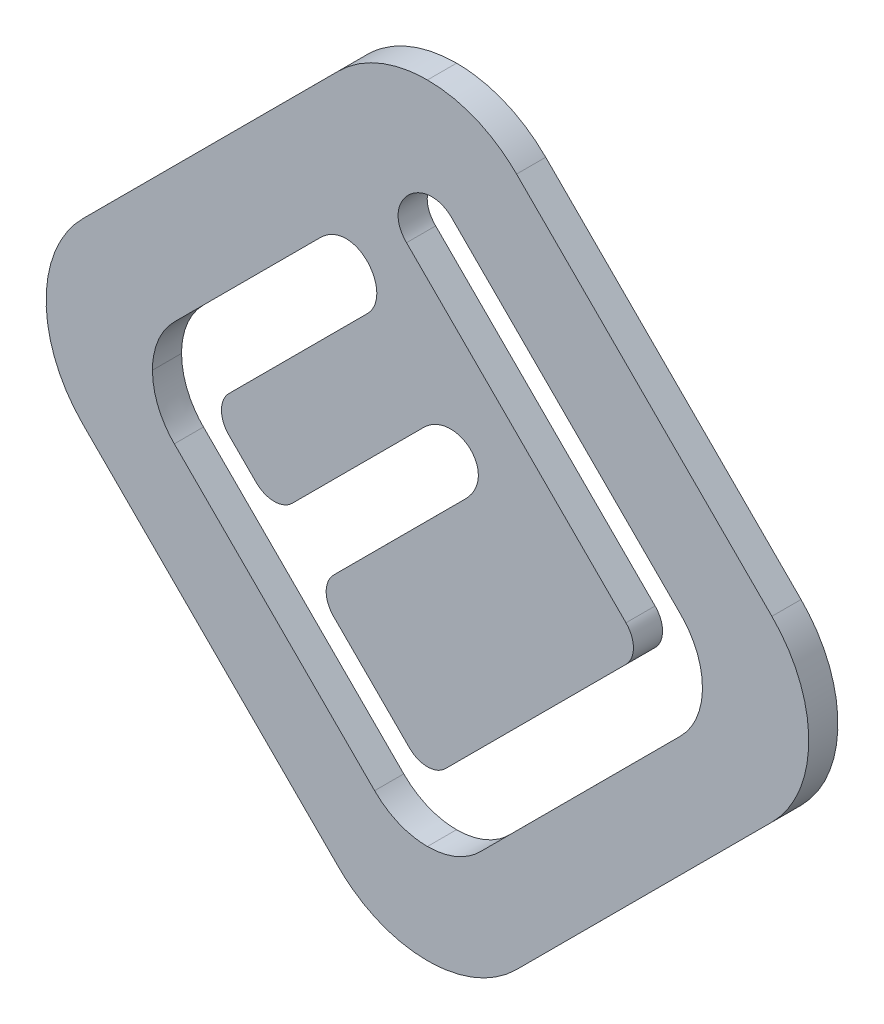
SolidWorks part; units mm, degrees
material "Maple"
ref_plane "Front Plane" through (0, 0, 0) normal (0, 0, 1) x (1, 0, 0)
ref_plane "Top Plane" through (0, 0, 0) normal (0, 1, 0) x (1, 0, 0)
ref_plane "Right Plane" through (0, 0, 0) normal (1, 0, 0) x (0, 0, -1)
sketch "Sketch1" plane through (0, 0, 317.1825) normal (0, 0, 1) x (1, 0, 0)
  line L8 (18.0256, -0.3675) -> (4.6642, 12.994)
  line L9 (-4.6636, 12.994) -> (-18.0256, -0.3674)
  line L10 (-18.0253, -9.6953) -> (-4.6635, -23.0569)
  line L11 (4.6641, -23.0569) -> (18.0256, -9.6953)
  line L12 (18.0256, -0.3675) -> (4.6642, 12.994)
  line L13 (-4.6636, 12.994) -> (-18.0256, -0.3674)
  line L14 (-18.0253, -9.6953) -> (-4.6635, -23.0569)
  line L15 (4.6641, -23.0569) -> (18.0256, -9.6953)
  line L22 (2.7642, -18.6667) -> (13.244, -8.1858)
  line L23 (10.3894, -6.365) -> (0.9434, -15.8112)
  line L24 (-0.9425, -15.8112) -> (-4.9072, -11.8463)
  line L25 (-8.9601, -7.7941) -> (-10.3892, -6.3639)
  line L26 (-13.2442, -8.1856) -> (-2.7641, -18.665)
  line L27 (2.7642, -18.6667) -> (13.244, -8.1858)
  line L28 (10.3894, -6.365) -> (0.9434, -15.8112)
  line L29 (-0.9425, -15.8112) -> (-4.9072, -11.8463)
  line L30 (-8.9601, -7.7941) -> (-10.3892, -6.3639)
  line L31 (-13.2442, -8.1856) -> (-2.7641, -18.665)
  arc A10 (-10.3887, -4.4783) -> (-10.3892, -6.3639) centre (-9.4459, -5.4213) ccw
  arc A11 (-10.3887, -4.4783) -> (-10.3892, -6.3639) centre (-9.4459, -5.4213) ccw
  arc A12 (10.3894, -6.365) -> (10.3894, -4.4792) centre (9.4465, -5.4221) ccw
  arc A13 (10.3894, -6.365) -> (10.3894, -4.4792) centre (9.4465, -5.4221) ccw
  arc A14 (-0.9425, -15.8112) -> (0.9434, -15.8112) centre (0.0004, -14.8683) ccw
  arc A15 (-0.9425, -15.8112) -> (0.9434, -15.8112) centre (0.0004, -14.8683) ccw
  arc A16 (-4.9072, -9.9604) -> (-4.9072, -11.8463) centre (-3.9643, -10.9034) ccw
  arc A17 (-4.9072, -9.9604) -> (-4.9072, -11.8463) centre (-3.9643, -10.9034) ccw
  arc A18 (-8.9601, -7.7941) -> (-7.074, -7.7946) centre (-8.0168, -6.8515) ccw
  arc A19 (-8.9601, -7.7941) -> (-7.074, -7.7946) centre (-8.0168, -6.8515) ccw
  spline S12 degree 3 poles (-2511.7582, 1599.7542) (-528.2673, 253.9159) (-9.7312, -51.3951) (18.9649, -8.5195) (19.0757, -8.335) (19.2797, -7.9533) (19.3731, -7.7556) (19.6204, -7.1566) (19.7443, -6.7455) (19.9118, -5.9003) (19.9545, -5.4636) (19.9548, -4.6035) (19.9137, -4.1758) (19.7883, -3.5377) (19.7358, -3.3259) (19.6114, -2.9129) (19.5394, -2.7105) (19.2943, -2.1153) (19.0909, -1.7324) (-37.9766, 83.7462) (-1962.1181, -1327.3743) (2142.1316, 2091.9164) knots -14.829429 -14.829429 -14.829429 -14.829429 0.125 0.125 0.1875 0.1875 0.25 0.25 0.375 0.375 0.5 0.5 0.625 0.625 0.6875 0.6875 0.75 0.75 0.875 0.875 30.319445 30.319445 30.319445 30.319445 only from (18.0256, -9.6953) to (18.0256, -0.3675)
  spline S13 degree 3 poles (2060.8953, 2183.1746) (-826.604, -1283.2725) (72.1685, -32.1264) (3.3032, 14.0591) (2.9215, 14.2633) (2.3277, 14.5093) (2.1257, 14.5816) (1.7134, 14.7064) (1.502, 14.759) (-86.1752, 32.0415) (-378.542, -1744.8324) (74.0715, 3001.3127) knots -47.307192 -47.307192 -47.307192 -47.307192 0.25 0.25 0.5 0.5 0.625 0.625 0.75 0.75 52.195751 52.195751 52.195751 52.195751 only from (4.6642, 12.994) to (0, 14.9261)
  spline S14 degree 3 poles (-78.0817, 3003.3809) (333.8216, -1520.6268) (80.4345, 30.9133) (-1.7154, 14.717) (-2.1295, 14.5915) (-2.7233, 14.3455) (-2.9172, 14.2537) (-3.297, 14.0503) (-3.4836, 13.9381) (-77.3799, -35.6424) (963.934, -1487.2019) (-2063.4916, 2177.5207) knots -47.780071 -47.780071 -47.780071 -47.780071 0.25 0.25 0.5 0.5 0.625 0.625 0.75 0.75 51.983733 51.983733 51.983733 51.983733 only from (0, 14.9261) to (-4.6636, 12.994)
  spline S15 degree 3 poles (2511.9151, -1609.5684) (525.6018, -262.2474) (9.6465, 41.2257) (-18.9646, -1.5433) (-19.0754, -1.7279) (-19.2794, -2.1096) (-19.3726, -2.3073) (-19.6198, -2.9063) (-19.7436, -3.3174) (-19.911, -4.1626) (-19.9537, -4.5992) (-19.954, -5.4592) (-19.9129, -5.887) (-19.7875, -6.525) (-19.735, -6.7368) (-19.6106, -7.1498) (-19.5387, -7.3522) (-19.2936, -7.9474) (-19.0903, -8.3302) (38.3197, -94.3506) (1986.0805, 1334.8913) (-2140.6233, -2103.2338) knots -14.790887 -14.790887 -14.790887 -14.790887 0.125 0.125 0.1875 0.1875 0.25 0.25 0.375 0.375 0.5 0.5 0.625 0.625 0.6875 0.6875 0.75 0.75 0.875 0.875 30.504686 30.504686 30.504686 30.504686 only from (-18.0256, -0.3674) to (-18.0253, -9.6953)
  spline S16 degree 3 poles (-2063.9812, -2189.6776) (858.5748, 1317.0828) (-73.3227, 22.8454) (-3.3029, -24.1221) (-2.9213, -24.3262) (-2.3275, -24.5722) (-2.1255, -24.6445) (-1.7132, -24.7692) (-1.5019, -24.8219) (85.8981, -42.0444) (376.7071, 1723.2924) (-75.0135, -3011.5304) knots -48.116601 -48.116601 -48.116601 -48.116601 0.25 0.25 0.5 0.5 0.625 0.625 0.75 0.75 52.038338 52.038338 52.038338 52.038338 only from (-4.6635, -23.0569) to (0, -24.9889)
  spline S17 degree 3 poles (77.0147, -3013.227) (-336.0144, 1523.9448) (-80.7831, -41.0487) (1.7155, -24.7797) (2.1297, -24.6541) (2.7235, -24.4081) (2.9174, -24.3163) (3.2972, -24.113) (3.4839, -24.0008) (76.6131, 25.0515) (-940.5057, 1445.3095) (2061.2859, -2190.3089) knots -47.981659 -47.981659 -47.981659 -47.981659 0.25 0.25 0.5 0.5 0.625 0.625 0.75 0.75 51.442351 51.442351 51.442351 51.442351 only from (0, -24.9889) to (4.6641, -23.0569)
  spline S18 degree 3 poles (18.0256, -9.6953) (18.3335, -9.3874) (18.6066, -9.0549) (18.9649, -8.5195) (19.0757, -8.335) (19.2797, -7.9533) (19.3731, -7.7556) (19.6204, -7.1566) (19.7443, -6.7455) (19.9118, -5.9003) (19.9545, -5.4636) (19.9548, -4.6035) (19.9137, -4.1758) (19.7883, -3.5377) (19.7358, -3.3259) (19.6114, -2.9129) (19.5394, -2.7105) (19.2943, -2.1153) (19.0909, -1.7324) (18.6084, -1.0097) (18.3335, -0.6754) (18.0256, -0.3675) knots 0 0 0 0 0.125 0.125 0.1875 0.1875 0.25 0.25 0.375 0.375 0.5 0.5 0.625 0.625 0.6875 0.6875 0.75 0.75 0.875 0.875 1 1 1 1
  spline S19 degree 3 poles (4.6642, 12.994) (4.3568, 13.3013) (4.0234, 13.5761) (3.3032, 14.0591) (2.9215, 14.2633) (2.3277, 14.5093) (2.1257, 14.5816) (1.7134, 14.7064) (1.502, 14.759) (0.8645, 14.8847) (0.4346, 14.9261) (0, 14.9261) knots 0 0 0 0 0.25 0.25 0.5 0.5 0.625 0.625 0.75 0.75 1 1 1 1
  spline S20 degree 3 poles (0, 14.9261) (-0.4346, 14.9261) (-0.8646, 14.8847) (-1.7154, 14.717) (-2.1295, 14.5915) (-2.7233, 14.3455) (-2.9172, 14.2537) (-3.297, 14.0503) (-3.4836, 13.9381) (-4.0232, 13.5761) (-4.3564, 13.3014) (-4.6636, 12.994) knots 0 0 0 0 0.25 0.25 0.5 0.5 0.625 0.625 0.75 0.75 1 1 1 1
  spline S21 degree 3 poles (-18.0256, -0.3674) (-18.3335, -0.6753) (-18.6065, -1.008) (-18.9646, -1.5433) (-19.0754, -1.7279) (-19.2794, -2.1096) (-19.3726, -2.3073) (-19.6198, -2.9063) (-19.7436, -3.3174) (-19.911, -4.1626) (-19.9537, -4.5992) (-19.954, -5.4592) (-19.9129, -5.887) (-19.7875, -6.525) (-19.735, -6.7368) (-19.6106, -7.1498) (-19.5387, -7.3522) (-19.2936, -7.9474) (-19.0903, -8.3302) (-18.608, -9.053) (-18.3331, -9.3874) (-18.0253, -9.6953) knots 0 0 0 0 0.125 0.125 0.1875 0.1875 0.25 0.25 0.375 0.375 0.5 0.5 0.625 0.625 0.6875 0.6875 0.75 0.75 0.875 0.875 1 1 1 1
  spline S22 degree 3 poles (-4.6635, -23.0569) (-4.3563, -23.3642) (-4.023, -23.6391) (-3.3029, -24.1221) (-2.9213, -24.3262) (-2.3275, -24.5722) (-2.1255, -24.6445) (-1.7132, -24.7692) (-1.5019, -24.8219) (-0.8644, -24.9475) (-0.4346, -24.9889) (0, -24.9889) knots 0 0 0 0 0.25 0.25 0.5 0.5 0.625 0.625 0.75 0.75 1 1 1 1
  spline S23 degree 3 poles (0, -24.9889) (0.4346, -24.9889) (0.8647, -24.9475) (1.7155, -24.7797) (2.1297, -24.6541) (2.7235, -24.4081) (2.9174, -24.3163) (3.2972, -24.113) (3.4839, -24.0008) (4.0235, -23.6388) (4.3568, -23.3641) (4.6641, -23.0569) knots 0 0 0 0 0.25 0.25 0.5 0.5 0.625 0.625 0.75 0.75 1 1 1 1
  spline S60 degree 3 poles (1176.9932, 2751.1582) (-176.5268, 17.7172) (5.8206, -26.8821) (14.1915, -6.6839) (14.2664, -6.4368) (28.4225, 65.3908) (-1979.9733, 384.6501) (3001.8471, -152.1386) knots -20.761237 -20.761237 -20.761237 -20.761237 0.5 0.5 0.75 0.75 71.875062 71.875062 71.875062 71.875062 only from (13.244, -8.1858) to (14.3901, -5.4213)
  spline S61 degree 3 poles (-1073.5702, 2784.6462) (-138.816, -121.7095) (22.3829, -23.9215) (13.9972, -3.69) (13.8753, -3.4624) (-25.8777, 55.709) (-1590.2116, -1079.6005) (2231.9739, 2004.1808) knots -20.803784 -20.803784 -20.803784 -20.803784 0.5 0.5 0.75 0.75 70.019049 70.019049 70.019049 70.019049 only from (14.3901, -5.4213) to (13.2442, -2.6577)
  spline S62 degree 3 poles (1817.1077, -2376.5506) (1405.8419, -1392.4468) (706.7276, -696.1701) (9.0468, 1.5399) (7.7528, 2.8339) (6.4588, 4.1279) (5.1649, 5.422) (-473.6749, 484.2923) (-951.6174, 964.06) (-93.2191, 2779.9556) knots -2.954135 -2.954135 -2.954135 -2.954135 0.005936 0.005936 0.005936 0.011426 0.011426 0.011426 2.043036 2.043036 2.043036 2.043036 only from (13.2442, -2.6577) to (1.283, 9.3041)
  spline S63 degree 3 poles (1802.3525, 2408.1127) (-116.4453, -205.8072) (14.1243, 0.6985) (0.9552, 9.5621) (0.8611, 9.6121) (0.6667, 9.6889) (0.5663, 9.7162) (0.3592, 9.7484) (0.2531, 9.7528) (-0.0594, 9.7337) (-0.2658, 9.6773) (-0.6454, 9.5) (-0.8196, 9.3797) (-1.1239, 9.0911) (-1.2525, 8.9245) (-1.3983, 8.647) (-1.4392, 8.5488) (-1.5001, 8.3491) (-1.5207, 8.2467) (-1.5389, 8.0362) (-1.5363, 7.9316) (-1.5071, 7.7256) (-1.4799, 7.6225) (2.8793, -3.4813) (150.6322, 47.4469) (-2666.4792, 1380.0713) knots -9.388184 -9.388184 -9.388184 -9.388184 0.0625 0.0625 0.125 0.125 0.1875 0.1875 0.25 0.25 0.375 0.375 0.5 0.5 0.625 0.625 0.6875 0.6875 0.75 0.75 0.8125 0.8125 0.875 0.875 7.92177 7.92177 7.92177 7.92177 only from (1.283, 9.3041) to (-1.0936, 7.0045)
  spline S64 degree 3 poles (864.2875, 2717.4029) (-613.4846, 622.5623) (-306.0488, 311.9816) (2.9477, 2.9624) (4.1879, 1.7221) (5.4282, 0.4818) (6.6685, -0.7585) (607.2081, -601.2824) (1212.8056, -1196.7484) (900.4702, -2710.0301) knots -1.305293 -1.305293 -1.305293 -1.305293 0.005716 0.005716 0.005716 0.010978 0.010978 0.010978 2.558819 2.558819 2.558819 2.558819 only from (-1.0936, 7.0045) to (10.3894, -4.4792)
  spline S69 degree 3 poles (-405.2513, -2770.8314) (-1061.8698, -1058.6776) (-530.0164, -535.0218) (-2.2375, -7.2911) (-1.5345, -6.5881) (-0.8315, -5.8852) (-0.1285, -5.1822) (187.032, 181.9735) (374.3822, 368.9402) (-1440.6601, 2557.7057) knots -2.235299 -2.235299 -2.235299 -2.235299 0.003775 0.003775 0.003775 0.006758 0.006758 0.006758 0.800802 0.800802 0.800802 0.800802 only from (-4.9072, -9.9604) to (1.9804, -3.0731)
  spline S70 degree 3 poles (2404.9504, -1798.6988) (-141.7149, 63.4455) (-5.595, -15.9122) (2.456, -2.4495) (2.5074, -2.347) (2.5896, -2.1361) (2.6209, -2.0278) (2.6793, -1.6923) (2.6683, -1.4614) (2.5646, -1.1366) (2.5168, -1.0345) (2.3951, -0.8429) (2.3214, -0.7547) (2.1564, -0.6003) (2.0629, -0.5325) (1.8655, -0.4219) (1.7603, -0.3782) (1.5414, -0.3149) (1.4301, -0.2958) (1.2039, -0.2809) (1.089, -0.2855) (0.7535, -0.3323) (0.535, -0.4084) (-12.271, -7.3798) (43.1582, -146.4989) (1088.5102, 2793.1968) knots -8.532385 -8.532385 -8.532385 -8.532385 0.125 0.125 0.1875 0.1875 0.25 0.25 0.375 0.375 0.4375 0.4375 0.5 0.5 0.5625 0.5625 0.625 0.625 0.6875 0.6875 0.75 0.75 0.875 0.875 8.813118 8.813118 8.813118 8.813118 only from (1.9804, -3.0731) to (-0.2049, -0.9265)
  spline S71 degree 3 poles (-1453.6171, 2555.5926) (366.3643, 367.2082) (182.8264, 182.0852) (-1.5136, -2.2353) (-2.4403, -3.1618) (-3.3671, -4.0884) (-4.2938, -5.0149) (-559.0423, -559.6573) (-1117.4085, -1110.6812) (-581.5927, -2756.0368) knots -0.780196 -0.780196 -0.780196 -0.780196 0.001851 0.001851 0.001851 0.005782 0.005782 0.005782 2.359156 2.359156 2.359156 2.359156 only from (-0.2049, -0.9265) to (-7.074, -7.7946)
  spline S74 degree 3 poles (362.4882, -2758.1519) (-813.5327, -787.4356) (-405.7984, -399.8155) (-8.0838, -2.174) (-7.262, -1.3524) (-6.4402, -0.5307) (-5.6185, 0.2911) (225.2785, 231.2089) (451.0333, 467.2704) (-1252.3612, 2629.9301) knots -1.683946 -1.683946 -1.683946 -1.683946 0.003259 0.003259 0.003259 0.006745 0.006745 0.006745 0.986403 0.986403 0.986403 0.986403 only from (-10.3887, -4.4783) to (-3.1537, 2.7567)
  spline S75 degree 3 poles (2411.6495, -1776.5621) (-276.5911, 150.4084) (-13.6507, -12.5996) (-2.8742, 3.1082) (-2.8191, 3.2079) (-2.7314, 3.4167) (-2.6991, 3.524) (-2.6575, 3.7445) (-2.6483, 3.859) (-2.6622, 4.4225) (-2.8654, 4.8658) (-3.2742, 5.2517) (-3.3652, 5.3218) (-3.5569, 5.4396) (-3.658, 5.488) (-3.9781, 5.5995) (-4.2075, 5.6248) (-4.5456, 5.5863) (-4.6555, 5.5613) (-4.8699, 5.4899) (-4.9744, 5.4432) (-17.4557, -1.4515) (42.9629, -138.0725) (23.4159, 3004.3315) knots -10.495558 -10.495558 -10.495558 -10.495558 0.0625 0.0625 0.125 0.125 0.1875 0.1875 0.25 0.25 0.5 0.5 0.5625 0.5625 0.625 0.625 0.75 0.75 0.8125 0.8125 0.875 0.875 8.745164 8.745164 8.745164 8.745164 only from (-3.1537, 2.7567) to (-5.6083, 4.9784)
  spline S76 degree 3 poles (2761.1279, 315.1185) (1020.8103, 1028.246) (505.5953, 516.1854) (-8.0407, 2.5459) (-8.908, 1.6787) (-9.7752, 0.8114) (-10.6425, -0.0558) (-691.6353, -681.0651) (-1370.8558, -1363.8466) (-2504.263, -1592.4357) knots -2.17574 -2.17574 -2.17574 -2.17574 0.00344 0.00344 0.00344 0.007119 0.007119 0.007119 2.896362 2.896362 2.896362 2.896362 only from (-5.6083, 4.9784) to (-13.2442, -2.6576)
  spline S77 degree 3 poles (-1215.392, -2745.4902) (177.2721, -28.8234) (-5.7997, 16.0783) (-14.1913, -4.1594) (-14.2662, -4.4065) (-27.869, -73.3911) (1825.9644, -370.692) (-3002.3381, 149.8994) knots -20.810204 -20.810204 -20.810204 -20.810204 0.5 0.5 0.75 0.75 69.064068 69.064068 69.064068 69.064068 only from (-13.2442, -2.6576) to (-14.39, -5.4217)
  spline S78 degree 3 poles (1077.1999, -2793.9083) (138.7417, 110.838) (-22.3816, 13.079) (-13.9971, -7.1532) (-13.8752, -7.3807) (26.1619, -66.9951) (1612.7826, 1084.786) (-2231.0608, -2015.8226) knots -20.803108 -20.803108 -20.803108 -20.803108 0.5 0.5 0.75 0.75 70.528658 70.528658 70.528658 70.528658 only from (-14.39, -5.4217) to (-13.2442, -8.1856)
  spline S79 degree 3 poles (2732.4808, -1237.8754) (23.6254, 172.167) (-21.5045, -11.2141) (-1.2625, -19.6127) (-1.0155, -19.6877) (65.4229, -32.7905) (344.083, 1686.6248) (-163.8985, -3008.0905) knots -20.814645 -20.814645 -20.814645 -20.814645 0.5 0.5 0.75 0.75 66.531019 66.531019 66.531019 66.531019 only from (-2.7641, -18.665) to (-0.0001, -19.8115)
  spline S80 degree 3 poles (2778.2255, 1097.5586) (-115.9559, 132.8617) (-18.471, -27.786) (1.7315, -19.4194) (1.9591, -19.2975) (64.5149, 22.6932) (-1205.8247, 1767.5334) (2016.8438, -2229.098) knots -20.76826 -20.76826 -20.76826 -20.76826 0.5 0.5 0.75 0.75 73.970917 73.970917 73.970917 73.970917 only from (-0.0001, -19.8115) to (2.7642, -18.6667)
  spline S81 degree 3 poles (13.244, -8.1858) (13.6088, -7.8219) (13.8997, -7.3881) (14.1915, -6.6839) (14.2664, -6.4368) (14.3656, -5.9336) (14.3901, -5.679) (14.3901, -5.4213) knots 0 0 0 0 0.5 0.5 0.75 0.75 1 1 1 1
  spline S82 degree 3 poles (14.3901, -5.4213) (14.3901, -4.9061) (14.289, -4.394) (13.9972, -3.69) (13.8753, -3.4624) (13.5894, -3.0369) (13.4265, -2.8396) (13.2442, -2.6577) knots 0 0 0 0 0.5 0.5 0.75 0.75 1 1 1 1
  spline S83 degree 3 poles (13.2442, -2.6577) (11.845, -1.2585) (10.4459, 0.1407) (9.0468, 1.5399) (7.7528, 2.8339) (6.4588, 4.1279) (5.1649, 5.422) (3.8709, 6.716) (2.577, 8.0101) (1.283, 9.3041) knots 0 0 0 0 0.005936 0.005936 0.005936 0.011426 0.011426 0.011426 0.016916 0.016916 0.016916 0.016916
  spline S84 degree 3 poles (1.283, 9.3041) (1.2085, 9.3788) (1.1282, 9.4457) (0.9552, 9.5621) (0.8611, 9.6121) (0.6667, 9.6889) (0.5663, 9.7162) (0.3592, 9.7484) (0.2531, 9.7528) (-0.0594, 9.7337) (-0.2658, 9.6773) (-0.6454, 9.5) (-0.8196, 9.3797) (-1.1239, 9.0911) (-1.2525, 8.9245) (-1.3983, 8.647) (-1.4392, 8.5488) (-1.5001, 8.3491) (-1.5207, 8.2467) (-1.5389, 8.0362) (-1.5363, 7.9316) (-1.5071, 7.7256) (-1.4799, 7.6225) (-1.365, 7.3297) (-1.2432, 7.1539) (-1.0936, 7.0045) knots 0 0 0 0 0.0625 0.0625 0.125 0.125 0.1875 0.1875 0.25 0.25 0.375 0.375 0.5 0.5 0.625 0.625 0.6875 0.6875 0.75 0.75 0.8125 0.8125 0.875 0.875 1 1 1 1
  spline S85 degree 3 poles (-1.0936, 7.0045) (0.2533, 5.657) (1.6005, 4.3097) (2.9477, 2.9624) (4.1879, 1.7221) (5.4282, 0.4818) (6.6685, -0.7585) (7.9088, -1.9987) (9.1491, -3.2389) (10.3894, -4.4792) knots 0 0 0 0 0.005716 0.005716 0.005716 0.010978 0.010978 0.010978 0.01624 0.01624 0.01624 0.01624
  spline S90 degree 3 poles (-4.9072, -9.9604) (-4.0173, -9.0706) (-3.1274, -8.1809) (-2.2375, -7.2911) (-1.5345, -6.5881) (-0.8315, -5.8852) (-0.1285, -5.1822) (0.5745, -4.4792) (1.2775, -3.7762) (1.9804, -3.0731) knots 0 0 0 0 0.003775 0.003775 0.003775 0.006758 0.006758 0.006758 0.00974 0.00974 0.00974 0.00974
  spline S91 degree 3 poles (1.9804, -3.0731) (2.1408, -2.9127) (2.2829, -2.739) (2.456, -2.4495) (2.5074, -2.347) (2.5896, -2.1361) (2.6209, -2.0278) (2.6793, -1.6923) (2.6683, -1.4614) (2.5646, -1.1366) (2.5168, -1.0345) (2.3951, -0.8429) (2.3214, -0.7547) (2.1564, -0.6003) (2.0629, -0.5325) (1.8655, -0.4219) (1.7603, -0.3782) (1.5414, -0.3149) (1.4301, -0.2958) (1.2039, -0.2809) (1.089, -0.2855) (0.7535, -0.3323) (0.535, -0.4084) (0.138, -0.6245) (-0.0437, -0.7654) (-0.2049, -0.9265) knots 0 0 0 0 0.125 0.125 0.1875 0.1875 0.25 0.25 0.375 0.375 0.4375 0.4375 0.5 0.5 0.5625 0.5625 0.625 0.625 0.6875 0.6875 0.75 0.75 0.875 0.875 1 1 1 1
  spline S92 degree 3 poles (-0.2049, -0.9265) (-0.6411, -1.3628) (-1.0774, -1.799) (-1.5136, -2.2353) (-2.4403, -3.1618) (-3.3671, -4.0884) (-4.2938, -5.0149) (-5.2205, -5.9415) (-6.1472, -6.868) (-7.074, -7.7946) knots 0 0 0 0 0.001851 0.001851 0.001851 0.005782 0.005782 0.005782 0.009714 0.009714 0.009714 0.009714
  spline S95 degree 3 poles (-10.3887, -4.4783) (-9.6204, -3.7102) (-8.8521, -2.9421) (-8.0838, -2.174) (-7.262, -1.3524) (-6.4402, -0.5307) (-5.6185, 0.2911) (-4.7968, 1.1129) (-3.9752, 1.9347) (-3.1537, 2.7567) knots 0 0 0 0 0.003259 0.003259 0.003259 0.006745 0.006745 0.006745 0.010232 0.010232 0.010232 0.010232
  spline S96 degree 3 poles (-3.1537, 2.7567) (-3.0733, 2.8371) (-3.001, 2.9233) (-2.8742, 3.1082) (-2.8191, 3.2079) (-2.7314, 3.4167) (-2.6991, 3.524) (-2.6575, 3.7445) (-2.6483, 3.859) (-2.6622, 4.4225) (-2.8654, 4.8658) (-3.2742, 5.2517) (-3.3652, 5.3218) (-3.5569, 5.4396) (-3.658, 5.488) (-3.9781, 5.5995) (-4.2075, 5.6248) (-4.5456, 5.5863) (-4.6555, 5.5613) (-4.8699, 5.4899) (-4.9744, 5.4432) (-5.2694, 5.2802) (-5.4477, 5.1388) (-5.6083, 4.9784) knots 0 0 0 0 0.0625 0.0625 0.125 0.125 0.1875 0.1875 0.25 0.25 0.5 0.5 0.5625 0.5625 0.625 0.625 0.75 0.75 0.8125 0.8125 0.875 0.875 1 1 1 1
  spline S97 degree 3 poles (-5.6083, 4.9784) (-6.4191, 4.1676) (-7.2299, 3.3568) (-8.0407, 2.5459) (-8.908, 1.6787) (-9.7752, 0.8114) (-10.6425, -0.0558) (-11.5097, -0.9231) (-12.3769, -1.7904) (-13.2442, -2.6576) knots 0 0 0 0 0.00344 0.00344 0.00344 0.007119 0.007119 0.007119 0.010799 0.010799 0.010799 0.010799
  spline S98 degree 3 poles (-13.2442, -2.6576) (-13.6086, -3.0218) (-13.8994, -3.4554) (-14.1913, -4.1594) (-14.2662, -4.4065) (-14.3654, -4.9095) (-14.39, -5.1641) (-14.39, -5.4217) knots 0 0 0 0 0.5 0.5 0.75 0.75 1 1 1 1
  spline S99 degree 3 poles (-14.39, -5.4217) (-14.39, -5.9369) (-14.2888, -6.4491) (-13.9971, -7.1532) (-13.8752, -7.3807) (-13.5893, -7.8064) (-13.4265, -8.0036) (-13.2442, -8.1856) knots 0 0 0 0 0.5 0.5 0.75 0.75 1 1 1 1
  spline S100 degree 3 poles (-2.7641, -18.665) (-2.4, -19.0296) (-1.9665, -19.3206) (-1.2625, -19.6127) (-1.0155, -19.6877) (-0.5124, -19.7869) (-0.2578, -19.8115) (-0.0001, -19.8115) knots 0 0 0 0 0.5 0.5 0.75 0.75 1 1 1 1
  spline S101 degree 3 poles (-0.0001, -19.8115) (0.5151, -19.812) (1.0274, -19.711) (1.7315, -19.4194) (1.9591, -19.2975) (2.3848, -19.0118) (2.5821, -18.849) (2.7642, -18.6667) knots 0 0 0 0 0.5 0.5 0.75 0.75 1 1 1 1
  dimension "D1" = 0.254
  dimension "D2" = 0.254
extrude "Inlay Profile" add sketch "Sketch1" against normal up to surface (1.524 mm away)
